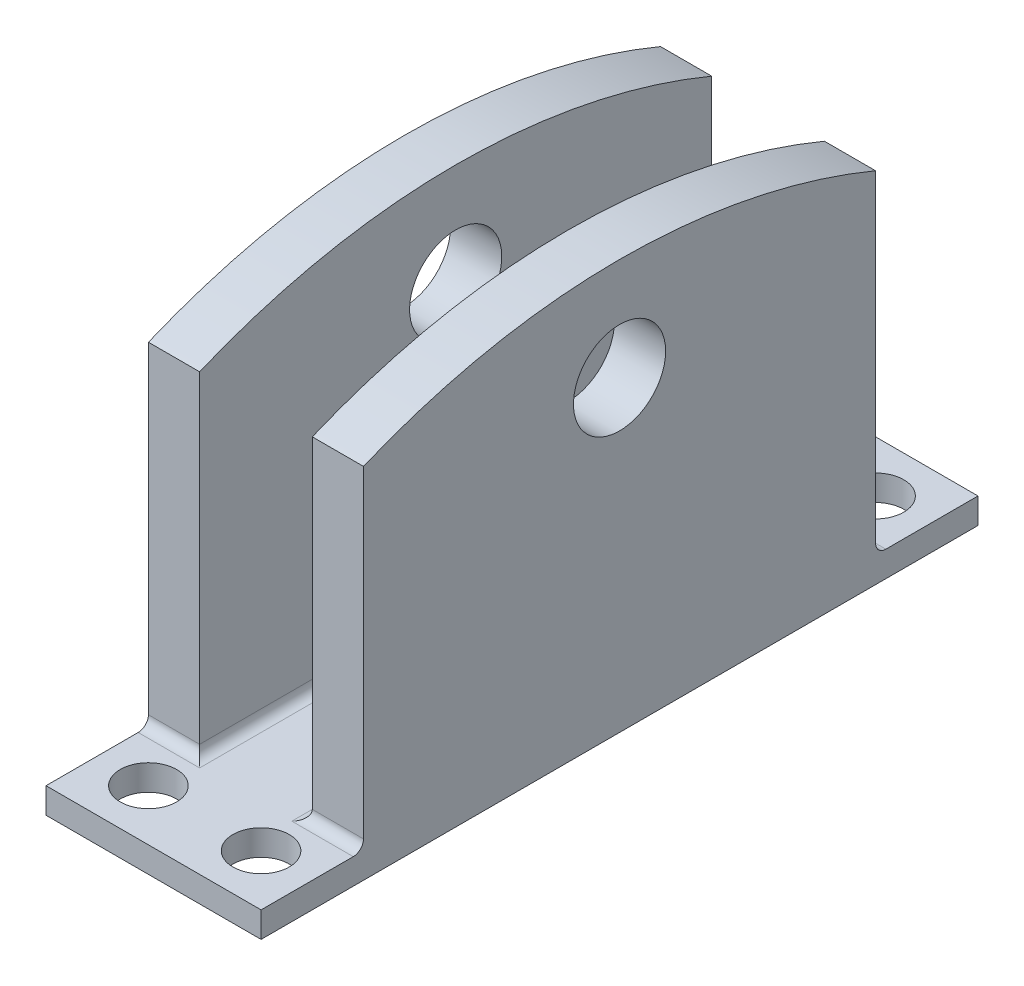
SolidWorks part; units mm, degrees
ref_plane "Front Plane" through (0, 0, 0) normal (0, 0, 1) x (1, 0, 0)
ref_plane "Top Plane" through (0, 0, 0) normal (0, 1, 0) x (1, 0, 0)
ref_plane "Right Plane" through (0, 0, 0) normal (1, 0, 0) x (0, 0, -1)
sketch "Sketch1" plane through (0, 0, 0) normal (0, 0, 1) x (1, 0, 0)
  line L0 (10.7535, 15.2985) -> (10.7535, 0) construction
  line L1 (0.2535, 50) -> (5.2535, 50)
  line L2 (0.2535, 50) -> (0.2535, 0)
  line L3 (0.2535, 0) -> (21.2535, 0)
  line L4 (21.2535, 50) -> (21.2535, 0)
  line L6 (5.2535, 50) -> (5.2535, 2.5)
  line L7 (5.2535, 2.5) -> (16.2535, 2.5)
  line L8 (16.2535, 50) -> (16.2535, 2.5)
  line L9 (16.2535, 50) -> (21.2535, 50)
  dimension "D1" = 21
  dimension "D2" = 11
  dimension "D3" = 2.5
  dimension "D4" = 50
extrude "Boss-Extrude1" add sketch "Sketch1" along normal blind 50
sketch "Sketch2" plane through (21.2535, 0, 0) normal (1, 0, 0) x (0, 0, -1)
  line L2 (-50, 35) -> (-50, 50)
  line L3 (-50, 50) -> (0, 50)
  line L4 (0, 50) -> (0, 35)
  line L5 (-50, 0) -> (0, 0) construction
  line L6 (-25, 50) -> (-25, 0) construction
  arc A0 (-50, 35) -> (0, 35) centre (-25, -25) cw
  point P4 (-25, 40)
  dimension "D1" = 35
  dimension "D2" = 40
extrude "Cut-Extrude1" cut sketch "Sketch2" against normal through all
sketch "Sketch3" plane through (21.2535, 0, 0) normal (1, 0, 0) x (0, 0, -1)
  line L1 (-25, 0) -> (-25, 40) construction
  line L2 (-50, 0) -> (0, 0) construction
  arc A0 (0, 35) -> (-50, 35) centre (-25, -25) ccw construction
  point P0 (-25, 30)
  dimension "D1" = 30
hole_wizard "M8 Clearance Hole1" positions "Sketch4" profile "Sketch5" hole size "M8" standard "BSI"
sketch "Sketch4" plane through (21.2535, 0, 0) normal (1, 0, 0) x (0, 0, -1)
  point P0 (-25, 30)
sketch "Sketch5" plane through (21.2535, 30, 25) normal (0, 1, 0) x (0, 0, -1)
  line L0 (0, 0) -> (0, 32.7039)
  line L1 (0, 32.7039) -> (4.5, 30)
  line L2 (4.5, 30) -> (4.5, 0)
  line L5 (4.5, 0) -> (0, 0)
  line L10 (0, 32.7039) -> (-4.5, 30) construction
  line L11 (0, -6.35) -> (0, 107.95) construction
  dimension "Hole Dia." = 9
  dimension "Hole Depth" = 30
  dimension "Drill Angle" = 118
sketch "Sketch6" plane through (0, 0, 0) normal (0, -1, 0) x (1, 0, 0)
  line L0 (0.2535, 50) -> (0.2535, 0) construction
  line L1 (21.2535, 0) -> (0.2535, 0)
  line L2 (21.2535, 0) -> (21.2535, -10)
  line L3 (21.2535, -10) -> (0.2535, -10)
  line L4 (0.2535, 0) -> (0.2535, -10)
  line L5 (21.2535, 25) -> (0.2535, 25) construction
  line L6 (21.2535, 50) -> (0.2535, 50)
  line L7 (0.2535, 50) -> (0.2535, 60)
  line L8 (21.2535, 60) -> (0.2535, 60)
  line L9 (21.2535, 50) -> (21.2535, 60)
  dimension "D1" = 10
extrude "Boss-Extrude2" add sketch "Sketch6" against normal blind 2.5
fillet "Fillet1" radius 1 6 edges at (16.2535, 2.5, 25) (5.2535, 2.5, 25) (18.7535, 2.5, 50) (2.7535, 2.5, 50) (2.7535, 2.5, 0) (18.7535, 2.5, 0)
sketch "Sketch7" plane through (0, 2.5, 0) normal (0, 1, 0) x (1, 0, 0)
  line L0 (10.7535, -60) -> (10.7535, 10) construction
  line L1 (21.2535, -60) -> (0.2535, -60) construction
  line L2 (0.2535, 10) -> (21.2535, 10) construction
  line L3 (0.2535, -60) -> (0.2535, -51) construction
  line L4 (0.2535, -25) -> (21.2535, -25) construction
  line L5 (0.2535, 0) -> (0.2535, -50) construction
  point P6 (5.2535, -55)
  point P7 (16.2535, 5)
  point P10 (5.2535, 5)
  point P17 (16.2535, -55)
  dimension "D1" = 5
  dimension "D2" = 5
hole_wizard "M5 Clearance Hole1" positions "Sketch8" profile "Sketch9" hole size "M5" standard "BSI" end condition through all
sketch "Sketch8" plane through (0, 2.5, 0) normal (0, 1, 0) x (1, 0, 0)
  point P0 (5.2535, -55)
  point P3 (16.2535, -55)
  point P6 (5.2535, 5)
  point P9 (16.2535, 5)
sketch "Sketch9" plane through (5.2535, 2.5, 55) normal (1, 0, 0) x (0, 0, 1)
  line L0 (0, 0) -> (0, 2.5)
  line L1 (0, 2.5) -> (2.75, 2.5)
  line L2 (2.75, 2.5) -> (2.75, 0)
  line L5 (2.75, 0) -> (0, 0)
  line L11 (0, -6.35) -> (0, 107.95) construction
  dimension "Thru Hole Dia." = 5.5
  dimension "Thru Hole Depth" = 2.5
